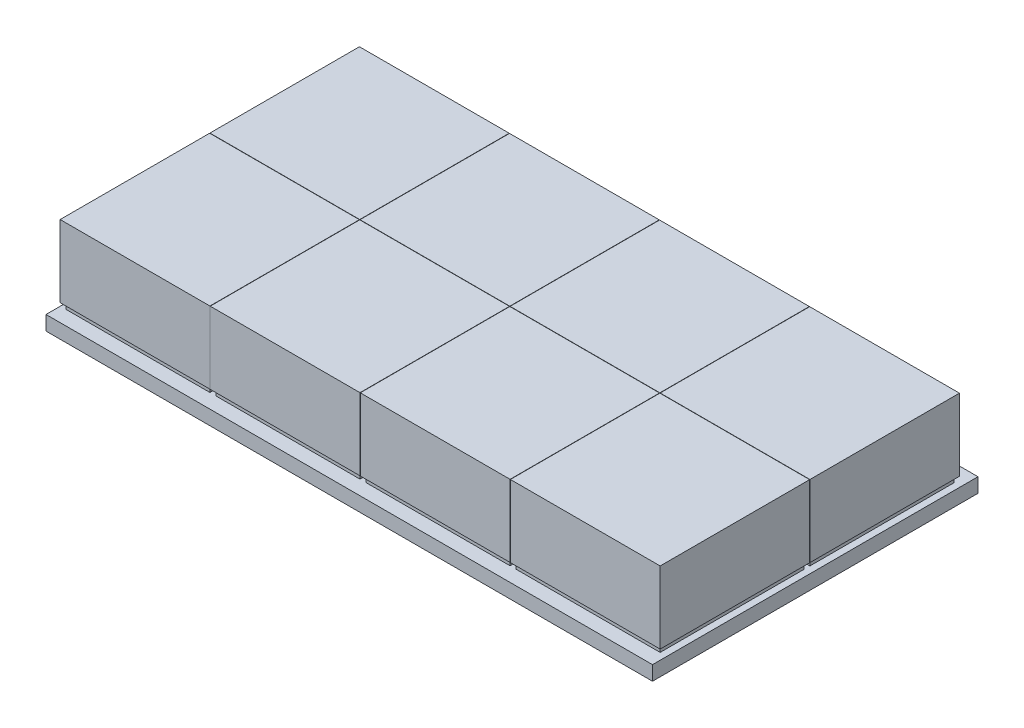
SolidWorks part; units mm, degrees
ref_plane "Front Plane" through (0, 0, 0) normal (0, 0, 1) x (1, 0, 0)
ref_plane "Top Plane" through (0, 0, 0) normal (0, 1, 0) x (1, 0, 0)
ref_plane "Right Plane" through (0, 0, 0) normal (1, 0, 0) x (0, 0, -1)
sketch "Sketch1" plane through (0, 0, 0) normal (0, 1, 0) x (1, 0, 0)
  line L1 (-250, -56.5) -> (250, -56.5)
  line L2 (-250, -56.5) -> (-250, 56.5)
  line L3 (-250, 56.5) -> (250, 56.5)
  line L4 (250, -56.5) -> (250, 56.5)
  line L5 (-250, -56.5) -> (250, 56.5) construction
  line L6 (-250, 56.5) -> (250, -56.5) construction
  point P0 (0, 0)
  dimension "D1" = 500
  dimension "D2" = 113
extrude "Boss-Extrude1" add sketch "Sketch1" along normal blind 5
sketch "Sketch2" plane through (0, 5, 0) normal (0, 1, 0) x (1, 0, 0)
  line L0 (0, 0) -> (0, -56.5) construction
  line L1 (-250, -56.5) -> (250, -56.5) construction
  line L3 (-25, -1.5) -> (25, -1.5)
  line L4 (-25, -1.5) -> (-25, -51.5)
  line L5 (-25, -51.5) -> (25, -51.5)
  line L6 (25, -1.5) -> (25, -51.5)
  line L7 (-25, -1.5) -> (25, -51.5) construction
  line L8 (-25, -51.5) -> (25, -1.5) construction
  point P5 (0, -26.5)
  dimension "D1" = 50
  dimension "D2" = 50
  dimension "D3" = 5
extrude "Boss-Extrude3" add sketch "Sketch2" along normal blind 2
pattern_linear "LPattern1" count 2 spacing 52 along (0, 0, -1) of "Boss-Extrude3"
sketch "Sketch3" plane through (0, 7, 0) normal (0, 1, 0) x (1, 0, 0)
  line L0 (0, 0) -> (0, -51.5) construction
  line L1 (-25, -51.5) -> (25, -51.5) construction
  line L3 (-26, -0.6) -> (26, -0.6)
  line L4 (-26, -0.6) -> (-26, -52.5)
  line L5 (-26, -52.5) -> (26, -52.5)
  line L6 (26, -0.6) -> (26, -52.5)
  line L7 (-26, -0.6) -> (26, -52.5) construction
  line L8 (-26, -52.5) -> (26, -0.6) construction
  line L9 (-250, -56.5) -> (250, -56.5) construction
  point P5 (0, -26.55)
  dimension "D1" = 52
  dimension "D2" = 51.9
  dimension "D3" = 4
extrude "Boss-Extrude8" add sketch "Sketch3" along normal blind 25
pattern_linear "LPattern5" count 2 spacing 52 along (0, 0, -1) of "Boss-Extrude8"
pattern_linear "LPattern6" count 4 spacing 52.1 along (1, 0, 0) of "Boss-Extrude3", "LPattern1", "Boss-Extrude8", "LPattern5"
sketch "Sketch4" plane through (0, 5, 0) normal (0, 1, 0) x (1, 0, 0)
  line L0 (250, 56.5) -> (-250, 56.5) construction
  line L1 (-26.9101, 56.5) -> (-250, 56.5)
  line L2 (-26.9101, 56.5) -> (-26.9101, -56.5)
  line L3 (-26.9101, -56.5) -> (-250, -56.5)
  line L4 (-250, 56.5) -> (-250, -56.5)
  line L6 (250, -56.5) -> (183.6449, -56.5)
  line L7 (250, -56.5) -> (250, 56.5)
  line L8 (250, 56.5) -> (183.6449, 56.5)
  line L9 (183.6449, -56.5) -> (183.6449, 56.5)
extrude "Cut-Extrude1" cut sketch "Sketch4" against normal blind 10
